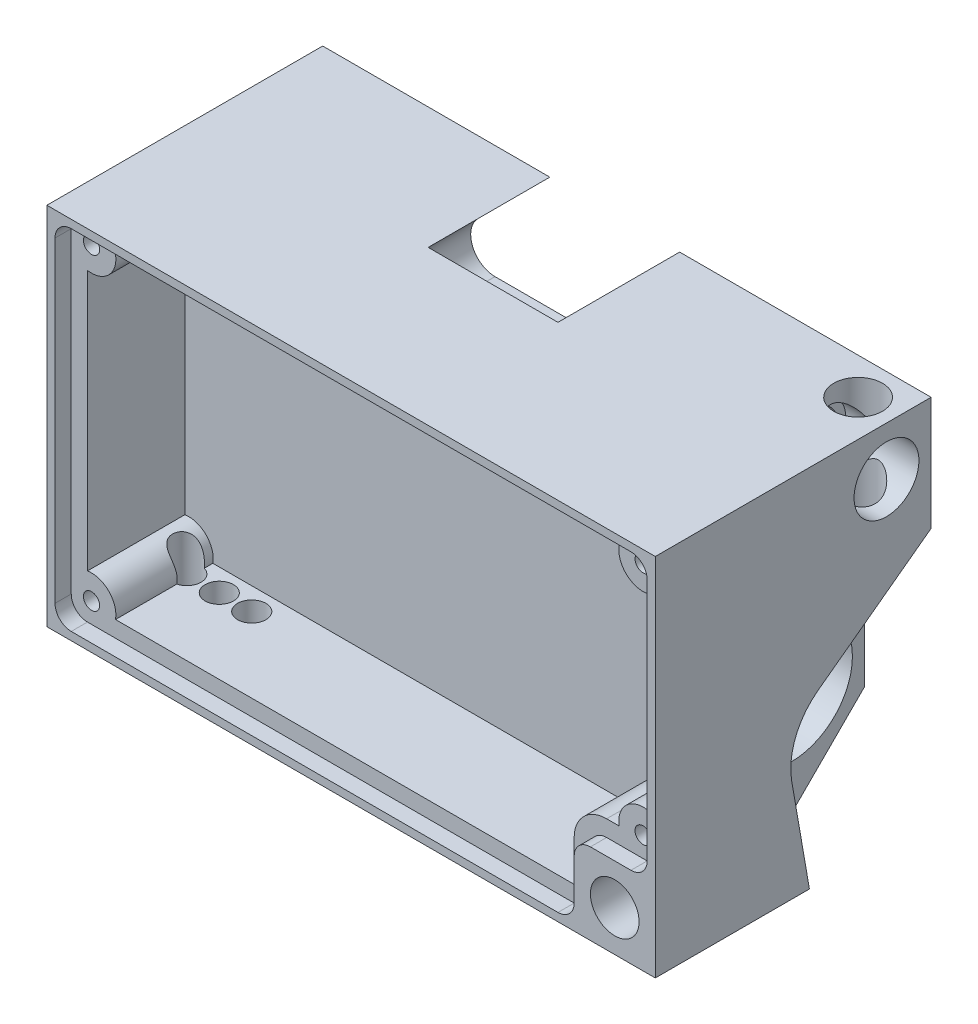
SolidWorks part; units mm, degrees
ref_plane "Front Plane" through (0, 0, 0) normal (0, 0, 1) x (1, 0, 0)
ref_plane "Top Plane" through (0, 0, 0) normal (0, 1, 0) x (1, 0, 0)
ref_plane "Right Plane" through (0, 0, 0) normal (1, 0, 0) x (0, 0, -1)
sketch "Sketch1" plane through (0, 0, 0) normal (1, 0, 0) x (0, 0, -1)
  line L0 (34, 10) -> (24, 0)
  line L1 (0, 0) -> (34, 0)
  line L2 (0, 0) -> (0, 45)
  line L3 (0, 45) -> (34, 45)
  line L4 (34, 0) -> (34, 45)
  dimension "D1" = 45
  dimension "D2" = 34
  dimension "D3" = 135
  dimension "D4" = 10
extrude "Boss-Extrude1" add sketch "Sketch1" against normal blind 75 contours L0 L4 L3 L2 L1
sketch "Sketch2" plane through (0, 0, 0) normal (1, 0, 0) x (0, 0, -1)
  line L0 (19, 0) -> (16.8216, 12.5843)
  line L1 (0, 0) -> (24, 0) construction
  line L2 (20.0583, 20.6685) -> (34, 31)
  line L3 (34, 10) -> (34, 45) construction
  line L4 (34, 31) -> (34, 0)
  line L5 (34, 0) -> (19, 0)
  line L6 (0, 45) -> (34, 45) construction
  line L7 (0, 0) -> (0, 45) construction
  arc A0 (16.8216, 12.5843) -> (20.0583, 20.6685) centre (25, 14) cw
  dimension "D5" = 8.3
  dimension "D1" = 14
  dimension "D2" = 19
  dimension "D3" = 25
  dimension "D4" = 14
extrude "Cut-Extrude1" cut sketch "Sketch2" against normal blind 8.2
sketch "Sketch3" plane through (0, 0, -34) normal (0, 0, -1) x (-1, 0, 0)
  line L0 (31, 45) -> (31, 31)
  line L1 (75, 45) -> (0, 45) construction
  line L2 (31, 31) -> (61, 31)
  line L3 (61, 31) -> (47, 45)
  line L4 (0, 31) -> (0, 45) construction
  line L5 (31, 45) -> (47, 45)
  dimension "D1" = 31
  dimension "D2" = 14
  dimension "D3" = 45
  dimension "D4" = 16
extrude "Cut-Extrude2" cut sketch "Sketch3" against normal blind 15
fillet "Fillet1" radius 3 2 edges at (-61, 31, -26.5) (-31, 31, -26.5)
sketch "Sketch5" plane through (0, 0, 0) normal (1, 0, 0) x (0, 0, -1)
  line L0 (0, 45) -> (34, 45) construction
  line L1 (34, 31) -> (34, 45) construction
  circle A0 centre (28.5, 39) radius 4
  dimension "D1" = 8
  dimension "D2" = 6
  dimension "D3" = 5.5
extrude "Cut-Extrude3" cut sketch "Sketch5" against normal blind 9
sketch "Sketch6" plane through (0, 45, 0) normal (0, 1, 0) x (1, 0, 0)
  line L0 (0, 0) -> (0, 34) construction
  line L1 (-31, 34) -> (0, 34) construction
  circle A0 centre (-4.5, 29.5) radius 3
  dimension "D1" = 6
  dimension "D2" = 4.5
  dimension "D3" = 4.5
extrude "Cut-Extrude4" cut sketch "Sketch6" against normal up to next
sketch "Sketch7" plane through (0, 0, 0) normal (0, 0, 1) x (1, 0, 0)
  line L0 (0, 0) -> (0, 45) construction
  line L1 (-75, 0) -> (0, 0) construction
  circle A0 centre (-5, 5) radius 3
  dimension "D1" = 6
  dimension "D2" = 5
  dimension "D3" = 5
extrude "Cut-Extrude5" cut sketch "Sketch7" against normal up to next
sketch "Sketch8" plane through (-8.2, 0, 0) normal (1, 0, 0) x (0, 0, -1)
  line L0 (0, 0) -> (0, 45) construction
  line L1 (0, 45) -> (34, 45) construction
  circle A0 centre (25, 14) radius 7.5
  arc A1 (20.0583, 20.6685) -> (16.8216, 12.5843) centre (25, 14) ccw construction
  point P6 (25, 14)
  point P10 (0, 0)
  dimension "D3" = 15
  dimension "D1" = 25
  dimension "D2" = 31
sketch "Sketch10" plane through (0, 45, 0) normal (0, 1, 0) x (1, 0, 0)
  circle A0 centre (-4.5, 29.5) radius 2.5
  circle A1 centre (-4.5, 29.5) radius 3 construction
  dimension "D1" = 5
extrude "Cut-Extrude7" cut sketch "Sketch10" against normal up to next
sketch "Sketch11" plane through (-9, 0, 0) normal (1, 0, 0) x (0, 0, -1)
  circle A0 centre (28.5, 39) radius 3
  dimension "D1" = 6
extrude "Cut-Extrude8" cut sketch "Sketch11" against normal up to next
sketch "Sketch13" plane through (0, 0, 0) normal (0, 0, 1) x (1, 0, 0)
  line L0 (-74, 44) -> (-74, 1)
  line L1 (-74, 1) -> (-10, 1)
  line L2 (-10, 1) -> (-10, 10)
  line L3 (-10, 10) -> (-1, 10)
  line L4 (-1, 10) -> (-1, 44)
  line L5 (-1, 44) -> (-74, 44)
  line L6 (-75, 45) -> (0, 45) construction
  line L7 (-75, 0) -> (-75, 45) construction
  line L8 (-75, 0) -> (0, 0) construction
  line L9 (0, 0) -> (0, 45) construction
  circle A0 centre (-5, 5) radius 3 construction
  dimension "D1" = 1
  dimension "D2" = 1
  dimension "D3" = 1
  dimension "D4" = 1
  dimension "D5" = 5
  dimension "D6" = 5
extrude "Cut-Extrude10" cut sketch "Sketch13" against normal blind 2
fillet "Fillet3" radius 2 6 edges at (-1, 44, -1) (-1, 10, -1) (-10, 10, -1) (-10, 1, -1) (-74, 1, -1) (-74, 44, -1)
sketch "Sketch14" plane through (0, 0, -2) normal (0, 0, 1) x (1, 0, 0)
  line L8 (0, 0) -> (0, 45) construction
  line L9 (-75, 45) -> (0, 45) construction
  line L10 (-75, 0) -> (-75, 45) construction
  line L11 (-75, 0) -> (0, 0) construction
  line L12 (-3, 12) -> (-3, 42)
  line L13 (-3, 42) -> (-72, 42)
  line L14 (-72, 42) -> (-72, 3)
  line L15 (-72, 3) -> (-12, 3)
  line L16 (-12, 3) -> (-12, 8)
  line L17 (-8, 12) -> (-3, 12)
  line L18 (-3, 12) -> (-3, 42)
  line L19 (-3, 42) -> (-72, 42)
  line L20 (-72, 42) -> (-72, 3)
  line L21 (-72, 3) -> (-12, 3)
  line L22 (-12, 3) -> (-12, 8)
  line L23 (-8, 12) -> (-3, 12)
  circle A6 centre (-3.5, 41.5) radius 1
  circle A7 centre (-71.5, 41.5) radius 1
  circle A8 centre (-71.5, 3.5) radius 1
  circle A9 centre (-3.5, 12.5) radius 1
  circle A10 centre (-71.5, 3.5) radius 3
  circle A11 centre (-71.5, 41.5) radius 3
  arc A12 (-8, 12) -> (-12, 8) centre (-8, 8) ccw
  arc A13 (-8, 12) -> (-12, 8) centre (-8, 8) ccw
  circle A14 centre (-3.5, 41.5) radius 3
  circle A15 centre (-3.5, 12.5) radius 3
  dimension "D4" = 2
  dimension "D5" = 2
  dimension "D8" = 2
  dimension "D11" = 2
  dimension "D2" = 3.5
  dimension "D3" = 3.5
  dimension "D6" = 3.5
  dimension "D7" = 3.5
  dimension "D9" = 3.5
  dimension "D10" = 3.5
  dimension "D12" = 3.5
  dimension "D13" = 12.5
  dimension "D1" = 2
  dimension "D14" = 2
extrude "Cut-Extrude11" cut sketch "Sketch14" against normal blind 12 contours A15 L18 A14 L19 A11 L20 A10 L21 L22 A13 L23
sketch "Sketch16" plane through (0, 0, 0) normal (0, -1, 0) x (1, 0, 0)
  line L0 (-75, 0) -> (0, 0) construction
  line L1 (-75, 0) -> (-75, -24) construction
  circle A0 centre (-69, -11.25) radius 1.75
  circle A1 centre (-65, -11.25) radius 1.75
  circle A2 centre (-61, -11.25) radius 1.75
  dimension "D1" = 3.5
  dimension "D2" = 11.25
  dimension "D3" = 6
  dimension "D4" = 3
extrude "Cut-Extrude12" cut sketch "Sketch16" against normal up to next
sketch "Sketch17" plane through (0, 0, -2) normal (0, 0, 1) x (1, 0, 0)
  circle A2 centre (-71.5, 41.5) radius 1
  circle A3 centre (-71.5, 3.5) radius 1
  circle A4 centre (-3.5, 12.5) radius 1
  circle A5 centre (-3.5, 41.5) radius 1
  dimension "D1" = 2
extrude "Cut-Extrude13" cut sketch "Sketch17" against normal blind 5
extrude "Cut-Extrude14" cut sketch "Sketch8" against normal blind 60
